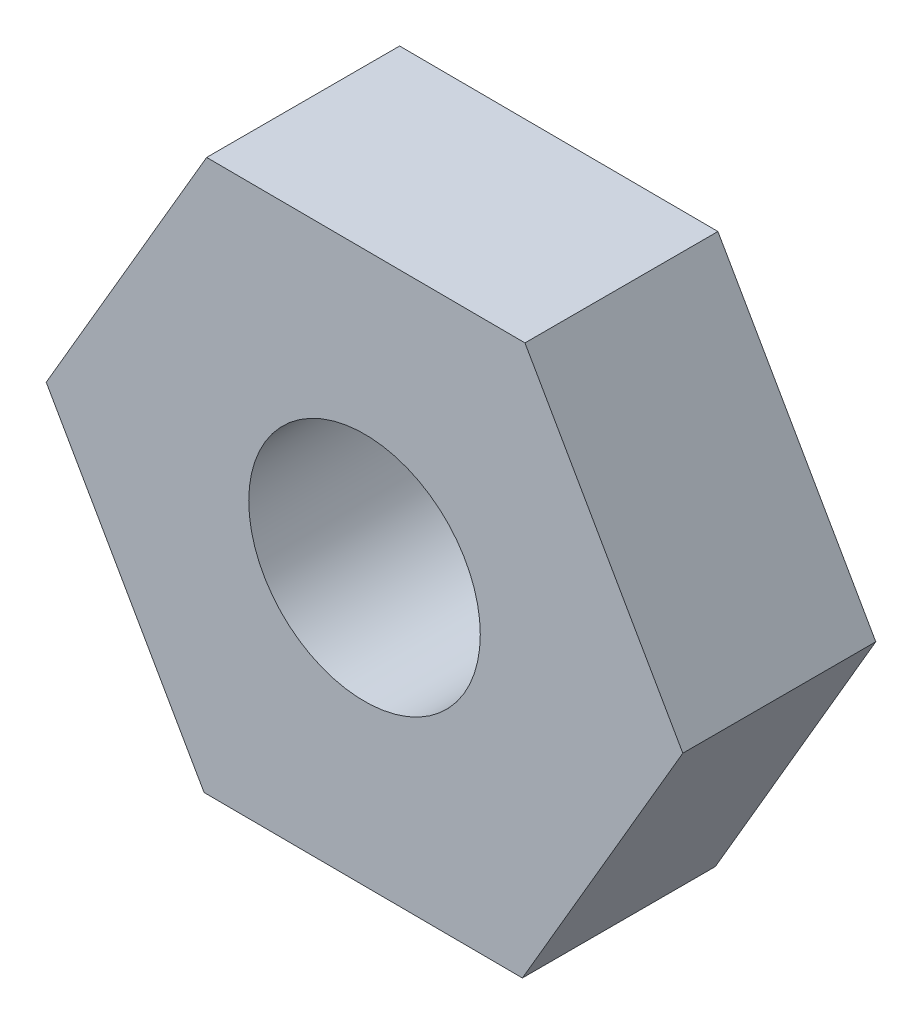
SolidWorks part; units mm, degrees
ref_plane "前视基准面" through (0, 0, 0) normal (0, 0, 1) x (1, 0, 0)
ref_plane "上视基准面" through (0, 0, 0) normal (0, 1, 0) x (1, 0, 0)
ref_plane "右视基准面" through (0, 0, 0) normal (1, 0, 0) x (0, 0, -1)
sketch "草图1" plane through (0, 0, 0) normal (0, 0, 1) x (1, 0, 0)
  line L1 (-2.8634, 5.0134) -> (-5.7734, 0.0269)
  line L2 (-5.7734, 0.0269) -> (-2.9101, -4.9865)
  line L3 (-2.9101, -4.9865) -> (2.8634, -5.0134)
  line L4 (2.8634, -5.0134) -> (5.7734, -0.0269)
  line L5 (5.7734, -0.0269) -> (2.9101, 4.9865)
  line L6 (2.9101, 4.9865) -> (-2.8634, 5.0134)
  circle A0 centre (0, 0) radius 5 construction
  circle A1 centre (0, 0) radius 2.1
  dimension "D1" = 4.2
  dimension "D2" = 10
extrude "凸台-拉伸1" add sketch "草图1" along normal blind 3.5
